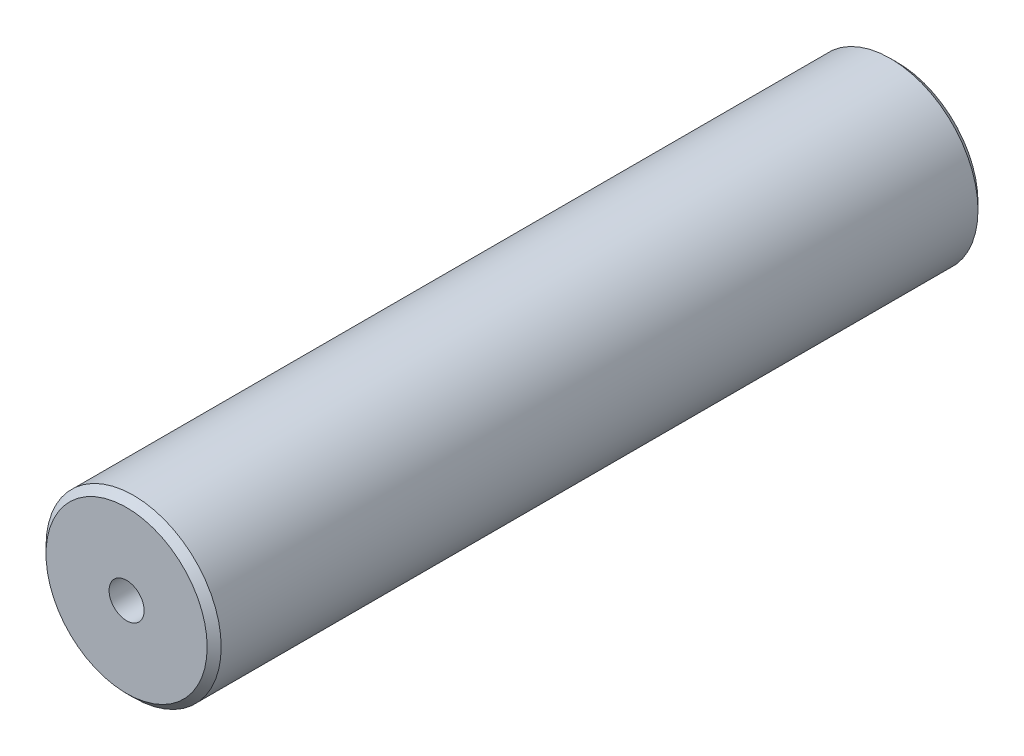
SolidWorks part; units mm, degrees
material "1.0545 (S355N)"
ref_plane "Front Plane" through (0, 0, 0) normal (0, 0, 1) x (1, 0, 0)
ref_plane "Top Plane" through (0, 0, 0) normal (0, 1, 0) x (1, 0, 0)
ref_plane "Right Plane" through (0, 0, 0) normal (1, 0, 0) x (0, 0, -1)
sketch "Sketch1" plane through (0, 0, 0) normal (0, 0, 1) x (1, 0, 0)
  circle A0 centre (0, 0) radius 12.5
  dimension "D1" = 25
extrude "Boss-Extrude1" add sketch "Sketch1" along normal mid plane 110
chamfer "Chamfer1" distance 1 angle 45 2 edges at (12.5, 0, -55) (12.5, 0, 55)
hole_wizard "M6 Tapped Hole1" positions "Sketch2" profile "Sketch4" tap size "M6" standard "ISO"
sketch "Sketch2" plane through (0, 0, 55) normal (0, 0, 1) x (1, 0, 0)
  point P0 (0, 0)
sketch "Sketch4" plane through (0, 0, 55) normal (1, 0, 0) x (0, -1, 0)
  line L0 (0, 0) -> (0, 16.5022)
  line L1 (0, 16.5022) -> (2.5, 15)
  line L2 (2.5, 15) -> (2.5, 0)
  line L5 (2.5, 0) -> (0, 0)
  line L10 (0, 16.5022) -> (-2.5, 15) construction
  line L11 (0, -6.35) -> (0, 107.95) construction
  dimension "Tap Drill Dia." = 5
  dimension "Tap Drill Depth" = 15
  dimension "Drill Angle" = 118
cosmetic thread "Hole Thread1" parameters "D1"=12, "D2"=6
mirror "Mirror1" about plane through (0, 0, 0) normal (0, 0, 1) of "M6 Tapped Hole1"
cosmetic thread "Hole Thread2" parameters "D1"=12, "D2"=6
